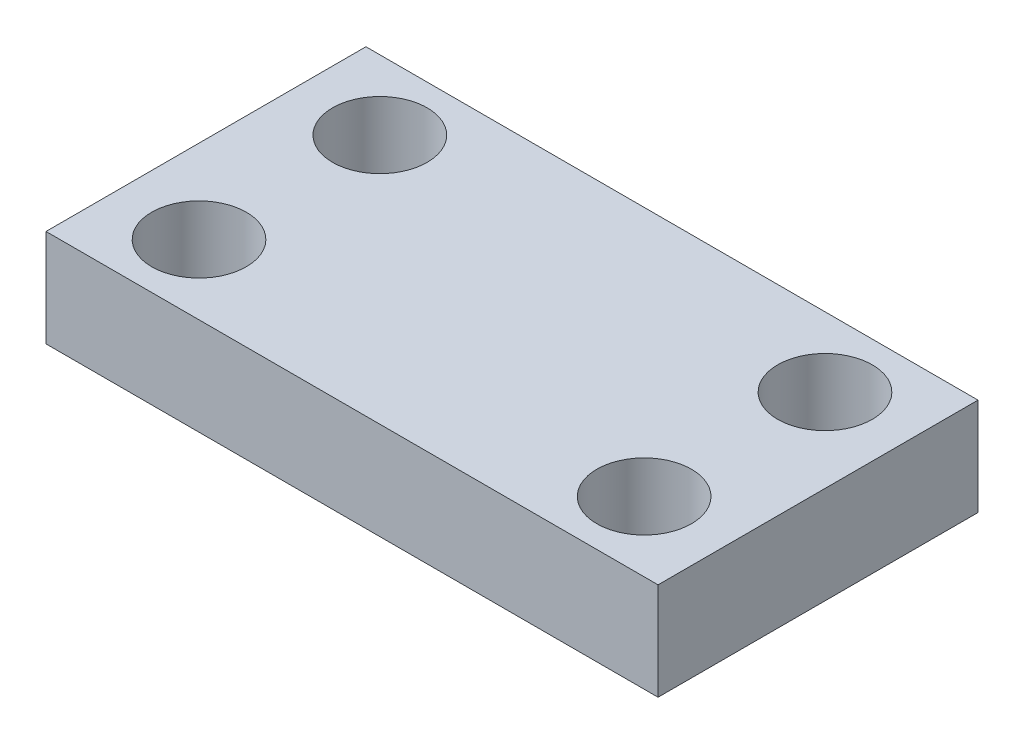
SolidWorks part; units mm, degrees
material "ABS PC"
ref_plane "Front Plane" through (0, 0, 0) normal (0, 0, 1) x (1, 0, 0)
ref_plane "Top Plane" through (0, 0, 0) normal (0, 1, 0) x (1, 0, 0)
ref_plane "Right Plane" through (0, 0, 0) normal (1, 0, 0) x (0, 0, -1)
sketch "Sketch1" plane through (0, 0, 0) normal (0, 1, 0) x (1, 0, 0)
  line L0 (0, 0) -> (0, 11.5)
  line L1 (0, 0) -> (22, 0)
  line L2 (0, 11.5) -> (22, 11.5)
  line L3 (22, 0) -> (22, 11.5)
  circle A0 centre (3, 2.5) radius 1.7
  circle A1 centre (3, 9) radius 1.7
  circle A2 centre (19, 9) radius 1.7
  circle A3 centre (19, 2.5) radius 1.7
  dimension "D1" = 3.4
  dimension "D2" = 16
  dimension "D3" = 6.5
  dimension "D4" = 2.5
  dimension "D7" = 3
  dimension "D5" = 2.5
  dimension "D6" = 3
extrude "Boss-Extrude1" add sketch "Sketch1" along normal blind 3.5
